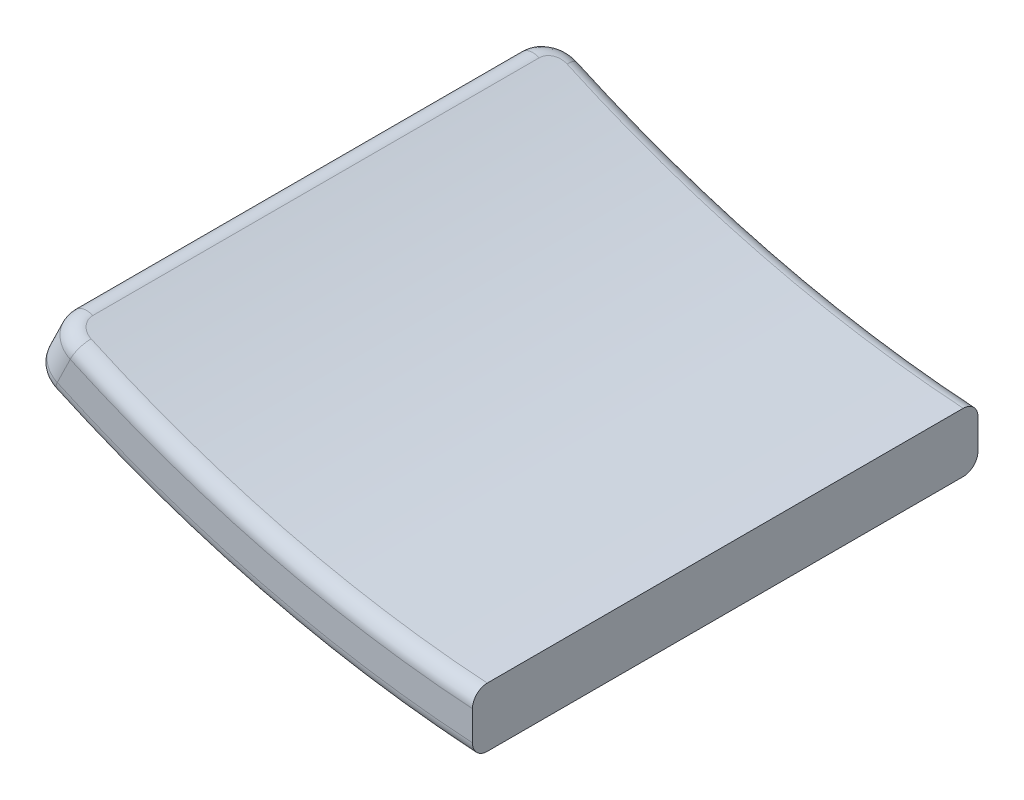
SolidWorks part; units mm, degrees
material "Polyurethane Foam Flexible"
ref_plane "Front Plane" through (0, 0, 0) normal (0, 0, 1) x (1, 0, 0)
ref_plane "Top Plane" through (0, 0, 0) normal (0, 1, 0) x (1, 0, 0)
ref_plane "Right Plane" through (0, 0, 0) normal (1, 0, 0) x (0, 0, -1)
sketch "Sketch1" plane through (0, 0, 0) normal (0, 0, 1) x (1, 0, 0)
  line L0 (-50.8, 241.8618) -> (-50.8, 190.9556)
  line L1 (-413.9908, 338.5903) -> (-436.2836, 292.943)
  line L2 (-50.8, -204.8629) -> (-50.8, 215.8246) construction
  line L4 (-38.1, -204.8629) -> (-38.1, -85.6629) construction
  arc A1 (-413.9908, 338.5903) -> (-50.8, 241.8618) centre (13.752, 1214.4469) ccw
  arc A2 (-436.2836, 292.943) -> (-50.8, 190.9556) centre (13.752, 1214.4469) ccw
  arc A3 (-436.2836, 292.943) -> (-0.1289, 189.0159) centre (13.752, 1214.4469) ccw construction
  arc A4 (-413.9908, 338.5903) -> (0.5587, 239.8112) centre (13.752, 1214.4469) ccw construction
  arc A5 (-413.9908, 338.5903) -> (-0.0449, 239.8196) centre (13.752, 1214.4469) ccw construction
  point P5 (0, 0)
  point P14 (-78.3876, 244.0866)
  point P15 (0, 0)
  dimension "D2" = 50.8
extrude "Boss-Extrude1" add sketch "Sketch1" against normal up to surface (434.6 mm away)
fillet "Fillet1" radius 25.4 2 edges at (-425.1372, 315.7666, 0) (-425.1372, 315.7666, -434.6)
fillet "Fillet2" radius 12.7 10 edges at (-236.2478, 219.8608, -434.6) (-431.2757, 290.5141, -425.0671) (-436.2836, 292.943, -217.3) (-427.6964, 288.7986, -5.5642) (-236.2478, 219.8608, 0) (-405.4024, 334.4478, -429.036) (-224.8073, 269.3658, -434.6) (-224.8073, 269.3658, 0) (-408.9826, 336.1621, -9.5329) (-413.9908, 338.5903, -217.3)
